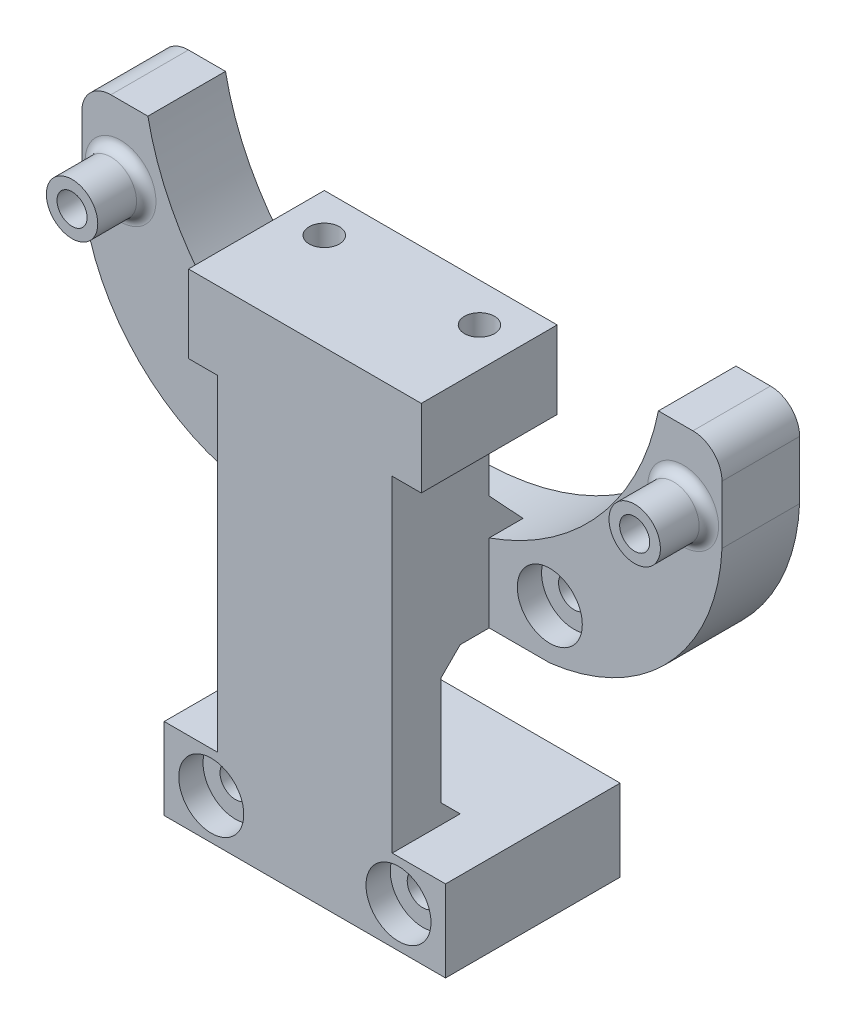
SolidWorks part; units mm, degrees
ref_plane "前视基准面" through (0, 0, 0) normal (0, 0, 1) x (1, 0, 0)
ref_plane "上视基准面" through (0, 0, 0) normal (0, 1, 0) x (1, 0, 0)
ref_plane "右视基准面" through (0, 0, 0) normal (1, 0, 0) x (0, 0, -1)
sketch "草图1" plane through (0, 0, 0) normal (0, 0, 1) x (1, 0, 0)
  line L0 (-31.7261, 22.6773) -> (-31.7261, 16.6773)
  line L1 (34.2739, 22.6773) -> (34.2739, 16.6773)
  line L2 (-28.7261, 25.6773) -> (-24.9088, 25.6773)
  line L3 (27.7171, 25.6773) -> (31.2739, 25.6773)
  line L5 (1.2739, -3.9227) -> (1.2739, 21.7436) construction
  line L6 (-13.9761, -2.4227) -> (16.5239, -2.4227)
  circle A0 centre (-13.9761, 2.6773) radius 1.6
  arc A1 (-28.7261, 25.6773) -> (-31.7261, 22.6773) centre (-28.7261, 22.6773) ccw
  circle A2 centre (16.5239, 2.6773) radius 1.6
  arc A3 (34.2739, 22.6773) -> (31.2739, 25.6773) centre (31.2739, 22.6773) ccw
  circle A4 centre (30.2739, 18.4773) radius 1.55
  arc A5 (-24.9088, 25.6773) -> (27.7171, 25.6773) centre (1.4042, 30.9398) ccw
  circle A6 centre (-27.7261, 18.4773) radius 1.55
  arc A7 (-31.7261, 16.6773) -> (-13.9761, -2.4227) centre (-11.5798, 17.6019) ccw
  arc A8 (16.5239, -2.4227) -> (34.2739, 16.6773) centre (14.1275, 17.6019) ccw
  point P25 (1.2739, -2.4227)
  dimension "D1" = 28.1
  dimension "D2" = 3.1
  dimension "D3" = 3.1
extrude "凸台-拉伸1" add sketch "草图1" along normal blind 8
sketch "草图2" plane through (0, 0, 8) normal (0, 0, 1) x (1, 0, 0)
  line L1 (-13.9761, -2.4227) -> (16.5239, -2.4227) construction
  line L2 (-7.7261, -17.5227) -> (-11.2261, -17.5227)
  line L4 (-7.7261, -2.4227) -> (-7.7261, 20.9273)
  line L5 (13.7739, -17.5227) -> (10.2739, -17.5227)
  line L6 (10.2739, -2.4227) -> (10.2739, 20.9273)
  line L8 (-7.7261, -2.4227) -> (-7.7261, -17.5227)
  line L9 (-7.7261, 20.9273) -> (-7.7261, 24.1273)
  line L10 (10.2739, -2.4227) -> (10.2739, -17.5227)
  line L11 (-7.7261, 24.1273) -> (10.2739, 24.1273)
  line L12 (-11.2261, -25.9227) -> (13.7739, -25.9227)
  line L13 (10.2739, 20.9273) -> (10.2739, 24.1273)
  line L14 (-11.2261, -17.5227) -> (-13.2261, -17.5227)
  line L16 (13.7739, -17.5227) -> (15.7739, -17.5227)
  line L17 (-13.2261, -17.5227) -> (-13.2261, -25.9227)
  line L18 (-13.2261, -25.9227) -> (-11.2261, -25.9227)
  line L19 (13.7739, -25.9227) -> (15.7739, -25.9227)
  line L20 (15.7739, -25.9227) -> (15.7739, -17.5227)
  circle A0 centre (10.9239, -21.7227) radius 1.6
  circle A1 centre (-8.3761, -21.7227) radius 1.6
  point P4 (-7.7261, -2.4227)
  point P12 (1.2739, -25.9227)
  point P13 (-11.2261, -25.9227)
  point P21 (13.7739, -17.5227)
  point P25 (10.9239, -21.7227)
  dimension "D5" = 2
  dimension "D10" = 3.2
  dimension "D11" = 3.2
  dimension "D1" = 3.2
  dimension "D2" = 18
  dimension "D3" = 23.35
  dimension "D4" = 2
extrude "凸台-拉伸2" add sketch "草图2" along normal blind 10
ref_plane "基准面1" through (0, 18.4773, 0) normal (0, -1, 0) x (-1, 0, 0)
sketch "草图4" plane through (0, 18.4773, 0) normal (0, -1, 0) x (-1, 0, 0)
  line L0 (-30.2739, 0) -> (-33.2739, 0)
  line L1 (-16.5239, 0) -> (-34.2739, 0) construction
  line L2 (-30.2739, -2.5) -> (-30.2739, -8) construction
  line L3 (-34.2739, -8) -> (-16.5239, -8) construction
  line L4 (-33.2739, 0) -> (-31.8239, -2.5)
  line L6 (-30.2739, -2.5) -> (-31.8239, -2.5)
  line L7 (-30.2739, 0) -> (-30.2739, -2.5)
  point P0 (-31.8239, 0)
  point P1 (-28.7239, 0)
  point P3 (-30.2739, 0)
  point P11 (-30.2739, -2.5)
  point P16 (-33.2739, 0)
  dimension "D1" = 1.55
  dimension "D2" = 2.5
  dimension "D3" = 3
revolve "切除-旋转4" cut sketch "草图4" angle 360 about L2
ref_plane "基准面2" through (1.2739, 0, 0) normal (1, 0, 0) x (0, 0, -1)
mirror "镜向1" about plane through (1.2739, 0, 0) normal (1, 0, 0) of "切除-旋转4"
sketch "草图5" plane through (0, 0, 8) normal (0, 0, 1) x (1, 0, 0)
  circle A0 centre (-27.7261, 18.4773) radius 2.65
  circle A1 centre (-27.7261, 18.4773) radius 1.55
  circle A2 centre (30.2739, 18.4773) radius 1.55
  circle A3 centre (30.2739, 18.4773) radius 2.65
  dimension "D1" = 5.3
  dimension "D2" = 5.3
extrude "凸台-拉伸3" add sketch "草图5" along normal blind 5
sketch "草图6" plane through (0, 0, 8) normal (0, 0, 1) x (1, 0, 0)
  circle A0 centre (-13.9761, 2.6773) radius 3.35
  circle A1 centre (16.5239, 2.6773) radius 3.35
  dimension "D1" = 6.7
  dimension "D2" = 6.7
extrude "切除-拉伸1" cut sketch "草图6" against normal blind 2.5
sketch "草图13" plane through (0, -25.9227, 0) normal (0, -1, 0) x (1, 0, 0)
  line L0 (-13.2261, 8) -> (-13.2261, 0)
  line L1 (-13.9761, 0) -> (16.5239, 0) construction
  line L2 (-13.2261, 0) -> (15.7739, 0)
  line L3 (15.7739, 0) -> (15.7739, 8)
  line L4 (15.7739, 8) -> (-13.2261, 8)
extrude "凸台-拉伸6" add sketch "草图13" against normal blind 8.4
sketch "草图14" plane through (0, 0, 0) normal (0, 0, -1) x (-1, 0, 0)
  circle A0 centre (-10.9239, -21.7227) radius 1.6
  circle A1 centre (8.3761, -21.7227) radius 1.6
extrude "切除-拉伸4" cut sketch "草图14" against normal through all
sketch "草图15" plane through (0, 0, 18) normal (0, 0, 1) x (1, 0, 0)
  circle A0 centre (-8.3761, -21.7227) radius 3.35
  circle A1 centre (10.9239, -21.7227) radius 3.35
  dimension "D1" = 6.7
  dimension "D2" = 6.7
extrude "切除-拉伸5" cut sketch "草图15" against normal blind 2.5
sketch "草图16" plane through (0, 24.1273, 0) normal (0, 1, 0) x (1, 0, 0)
  line L0 (-7.7261, -18) -> (-10.7261, -18)
  line L1 (-10.7261, -18) -> (-10.7261, -8)
  line L2 (-10.7261, -8) -> (-10.7261, -3.9907)
  line L3 (13.2739, -8) -> (13.2739, -18)
  line L4 (13.2739, -18) -> (-7.7261, -18)
  line L5 (-10.7261, -3.9907) -> (13.2739, -3.9907)
  line L6 (13.2739, -3.9907) -> (13.2739, -8)
  dimension "D1" = 3
  dimension "D2" = 24
extrude "凸台-拉伸7" add sketch "草图16" against normal blind 8
sketch "草图20" plane through (0, 24.1273, 0) normal (0, 1, 0) x (1, 0, 0)
  line L0 (10.2739, -8) -> (-7.7261, -8) construction
  line L1 (1.2739, -5.5) -> (1.2739, 5.5) construction
  circle A0 centre (-6.7261, -8) radius 1.55
  circle A1 centre (9.2739, -8) radius 1.55
  dimension "D2" = 3.1
  dimension "D4" = 3.1
  dimension "D1" = 8
  dimension "D3" = 8
extrude "切除-拉伸7" cut sketch "草图20" against normal blind 5
chamfer "倒角2" distance 3.5 distance2 3.5 1 edges at (1.2659, 4.1061, 8)
chamfer "倒角3" distance 1.5 distance2 1.5 1 edges at (1.2739, 16.1273, 8)
sketch "草图21" plane through (10.2739, 0, 0) normal (1, 0, 0) x (0, 0, -1)
  line L0 (-8, -2.4227) -> (-12.9899, -2.4227)
  line L1 (-12.9899, -2.4227) -> (-12.9899, -17.5227)
  line L2 (-18, -17.5227) -> (0, -17.5227) construction
  line L3 (-12.9899, -17.5227) -> (-8, -17.5227)
  line L4 (-8, -17.5227) -> (-8, -2.4227)
extrude "切除-拉伸8" cut sketch "草图21" against normal blind 26
chamfer "倒角5" distance 2 angle 45 2 edges at (1.2739, -17.5227, 12.9899) (1.2739, -2.4227, 12.9899)
fillet "圆角1" radius 1 2 edges at (32.9239, 18.4773, 8) (-25.0761, 18.4773, 8)
sketch "草图22" plane through (0, 0, 13) normal (0, 0, 1) x (1, 0, 0)
